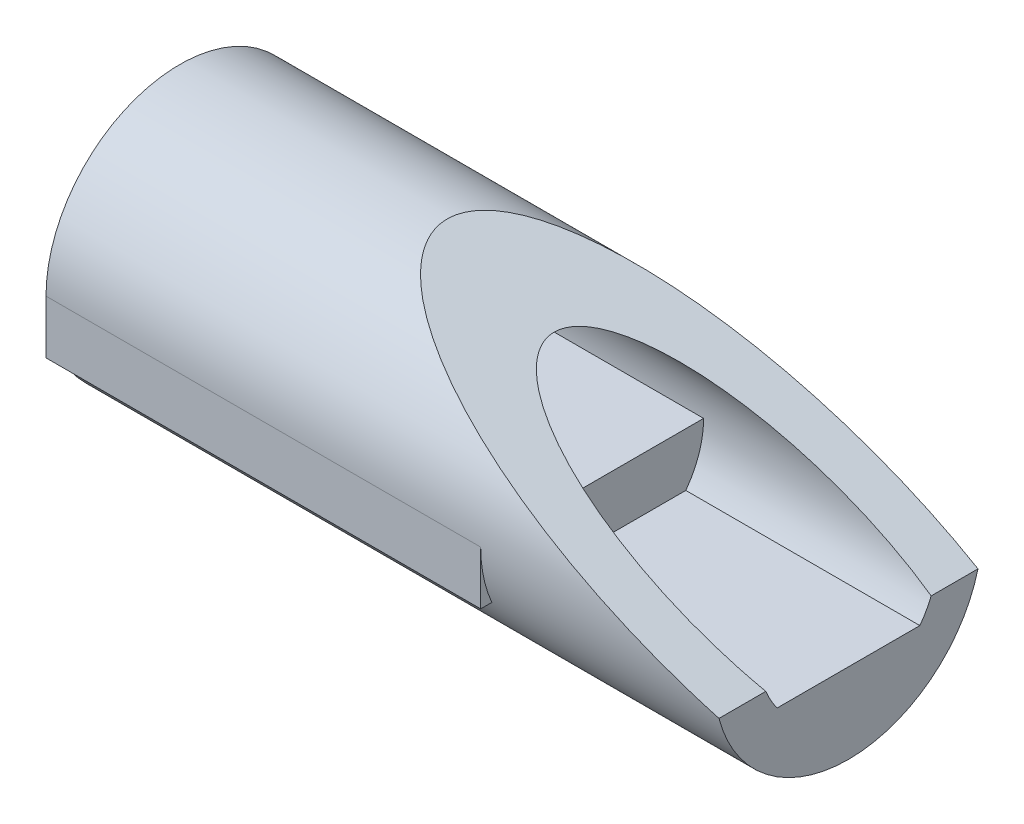
SolidWorks part; units mm, degrees
material "Brass"
ref_plane "Front Plane" through (0, 0, 0) normal (0, 0, 1) x (1, 0, 0)
ref_plane "Top Plane" through (0, 0, 0) normal (0, 1, 0) x (1, 0, 0)
ref_plane "Right Plane" through (0, 0, 0) normal (1, 0, 0) x (0, 0, -1)
sketch "Sketch1" plane through (0, 0, 0) normal (1, 0, 0) x (0, 0, -1)
  line L0 (19.3649, -5) -> (12.3649, -5)
  line L1 (-10.672, -8) -> (10.672, -8)
  line L2 (-12.3649, -5) -> (-19.3649, -5)
  circle A0 centre (0, 0) radius 20
  arc A1 (10.672, -8) -> (-10.672, -8) centre (0, 0) ccw
  point P4 (12.3649, -5)
  point P7 (0, -20)
  dimension "D1" = 40
  dimension "D2" = 7
  dimension "D3" = 15
  dimension "D4" = 12
extrude "Boss-Extrude1" add sketch "Sketch1" against normal blind 100 contours A1 L2 A0 L0 L1
sketch "Sketch2" plane through (0, -8, 0) normal (0, 1, 0) x (1, 0, 0)
  line L0 (-35, 10.672) -> (-35, -10.672)
  line L1 (-35, 10.672) -> (-35, 20)
  line L2 (0, 20) -> (-100, 20) construction
  line L3 (-35, 20) -> (-100, 20)
  line L4 (0, -10.672) -> (0, 10.672)
  line L5 (0, 10.672) -> (-100, 10.672)
  line L6 (-100, 10.672) -> (-100, -10.672)
  line L7 (-100, -10.672) -> (0, -10.672)
  line L8 (0, -10.672) -> (0, 10.672)
  line L9 (0, 10.672) -> (-100, 10.672)
  line L10 (-100, 10.672) -> (-100, -10.672)
  line L11 (-100, -10.672) -> (0, -10.672)
  line L12 (-100, 20) -> (-100, 10.672)
  line L13 (-35, -10.672) -> (-35, -20)
  line L14 (-100, -20) -> (0, -20) construction
  line L15 (-35, -20) -> (-100, -20)
  line L16 (-100, -20) -> (-100, -10.672)
  line M6 (0, 10.672) -> (-100, 10.672)
  line M7 (-100, 10.672) -> (-100, -10.672)
  line M8 (-100, -10.672) -> (0, -10.672)
  dimension "D2" = 35
  dimension "D1" = 0
extrude "Boss-Extrude2" add sketch "Sketch2" along normal blind 8 contours L3 L12 L1 M6 | L0 M6 M7 M8 | L16 L15 L13 M8
sketch "Sketch3" plane through (0, 0, 0) normal (0, 0, 1) x (1, 0, 0)
  line L0 (-100, 20) -> (-100, -20) construction
  line L1 (0, -20) -> (0, 20) construction
  line L2 (-100, -20) -> (0, -20) construction
  line L3 (0, 20) -> (-100, 20) construction
  line L4 (-100, 20) -> (-100, -20)
  line L5 (0, -20) -> (0, 20)
  line L6 (-100, -20) -> (0, -20)
  line L7 (0, 20) -> (-100, 20)
  line L8 (0, -5) -> (-60, 20)
  line L9 (0, -20) -> (0, -5)
  dimension "D1" = 40
  dimension "D2" = 15
extrude "Cut-Extrude2" cut sketch "Sketch3" against normal through all both and the other way through all contours L8 L5 L7
